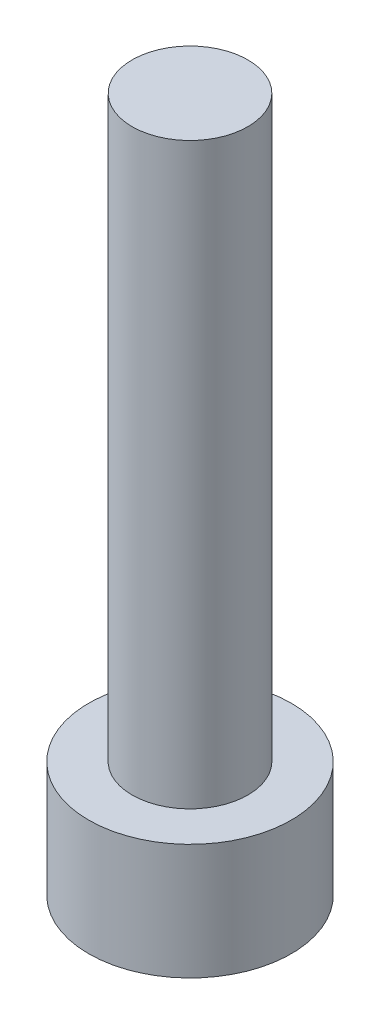
SolidWorks part; units mm, degrees
ref_plane "Front Plane" through (0, 0, 0) normal (0, 0, 1) x (1, 0, 0)
ref_plane "Top Plane" through (0, 0, 0) normal (0, 1, 0) x (1, 0, 0)
ref_plane "Right Plane" through (0, 0, 0) normal (1, 0, 0) x (0, 0, -1)
sketch "Sketch1" plane through (0, 0, 0) normal (0, 1, 0) x (1, 0, 0)
  circle A0 centre (0, 0) radius 3.5
  dimension "D1" = 7
extrude "Boss-Extrude1" add sketch "Sketch1" along normal blind 4
sketch "Sketch2" plane through (0, 4, 0) normal (0, 1, 0) x (1, 0, 0)
  circle A0 centre (0, 0) radius 2
  dimension "D1" = 4
extrude "Boss-Extrude2" add sketch "Sketch2" along normal blind 20
